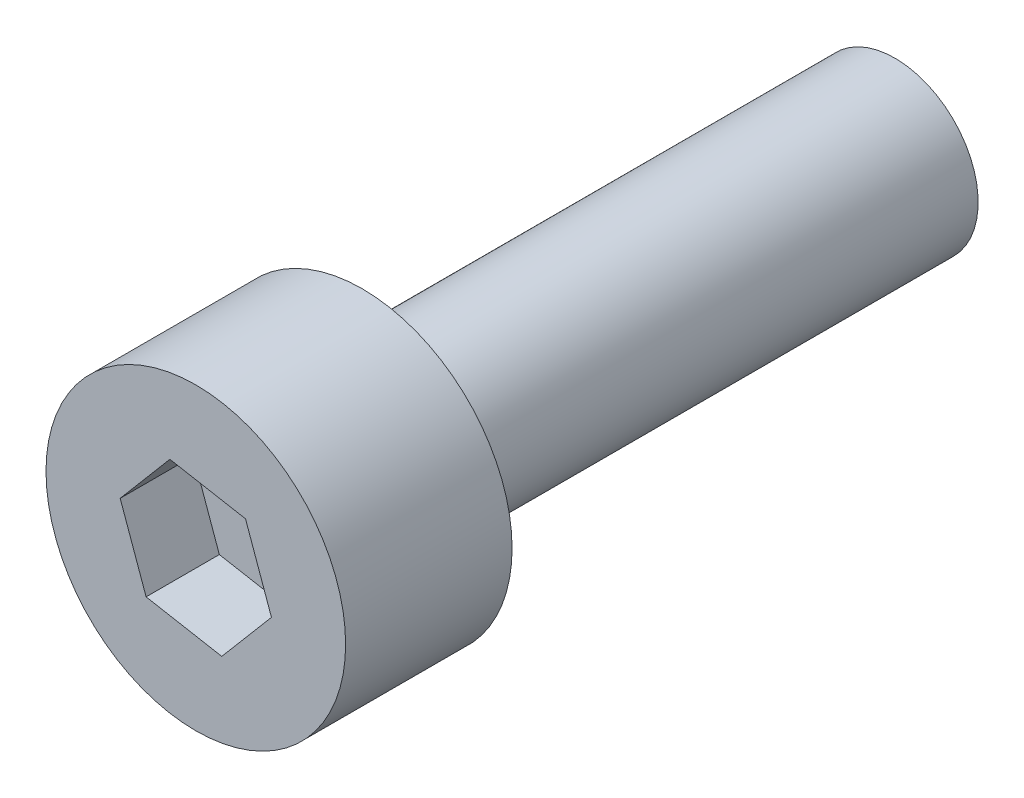
SolidWorks part; units mm, degrees
ref_plane "前视基准面" through (0, 0, 0) normal (0, 0, 1) x (1, 0, 0)
ref_plane "上视基准面" through (0, 0, 0) normal (0, 1, 0) x (1, 0, 0)
ref_plane "右视基准面" through (0, 0, 0) normal (1, 0, 0) x (0, 0, -1)
sketch "草图1" plane through (0, 0, 0) normal (0, 0, 1) x (1, 0, 0)
  circle A0 centre (0, 0) radius 2.25
  dimension "D1" = 4.5
extrude "凸台-拉伸1" add sketch "草图1" along normal blind 2.5
sketch "草图2" plane through (0, 0, 2.5) normal (0, 0, 1) x (1, 0, 0)
  line L1 (1.1362, -0.2061) -> (0.7466, 0.8809)
  line L2 (0.7466, 0.8809) -> (-0.3896, 1.087)
  line L3 (-0.3896, 1.087) -> (-1.1362, 0.2061)
  line L4 (-1.1362, 0.2061) -> (-0.7466, -0.8809)
  line L5 (-0.7466, -0.8809) -> (0.3896, -1.087)
  line L6 (0.3896, -1.087) -> (1.1362, -0.2061)
  circle A0 centre (0, 0) radius 1 construction
  circle A1 centre (0, 0) radius 2.25
  circle A2 centre (0, 0) radius 2.25
  dimension "D2" = 2
  dimension "D1" = 0
extrude "切除-拉伸1" cut sketch "草图2" against normal blind 1.1 contours L5 L6 L1 L2 L3 L4
sketch "草图3" plane through (0, 0, 0) normal (0, 0, -1) x (-1, 0, 0)
  circle A0 centre (0, 0) radius 1.25
  circle A1 centre (0, 0) radius 2.25
  circle A2 centre (0, 0) radius 2.25
  dimension "D2" = 2.5
  dimension "D1" = 0
extrude "凸台-拉伸2" add sketch "草图3" along normal blind 8 contours A0
